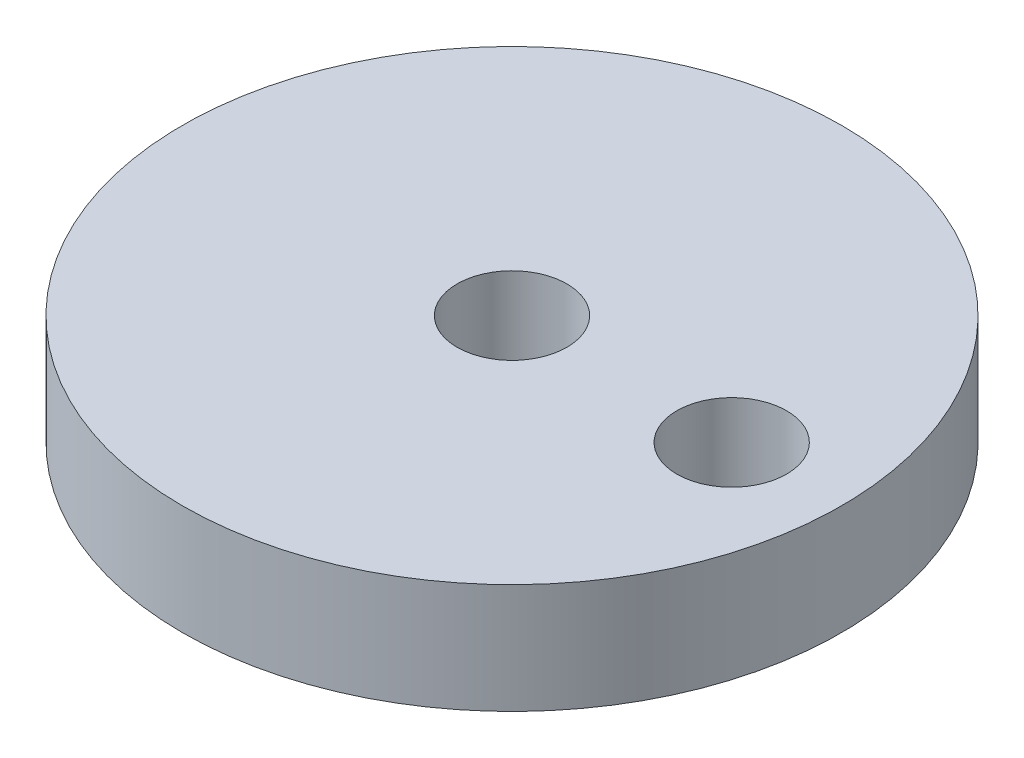
SolidWorks part; units mm, degrees
ref_plane "Front Plane" through (0, 0, 0) normal (0, 0, 1) x (1, 0, 0)
ref_plane "Top Plane" through (0, 0, 0) normal (0, 1, 0) x (1, 0, 0)
ref_plane "Right Plane" through (0, 0, 0) normal (1, 0, 0) x (0, 0, -1)
sketch "Sketch1" plane through (0, 0, 0) normal (0, 1, 0) x (1, 0, 0)
  line L0 (0, 0) -> (30, 0) construction
  circle A0 centre (0, 0) radius 30
  circle A1 centre (0, 0) radius 5
  circle A2 centre (20, 0) radius 5
  dimension "D1" = 60
  dimension "D2" = 10
  dimension "D3" = 20
  dimension "D4" = 10
extrude "Boss-Extrude1" add sketch "Sketch1" along normal blind 10
